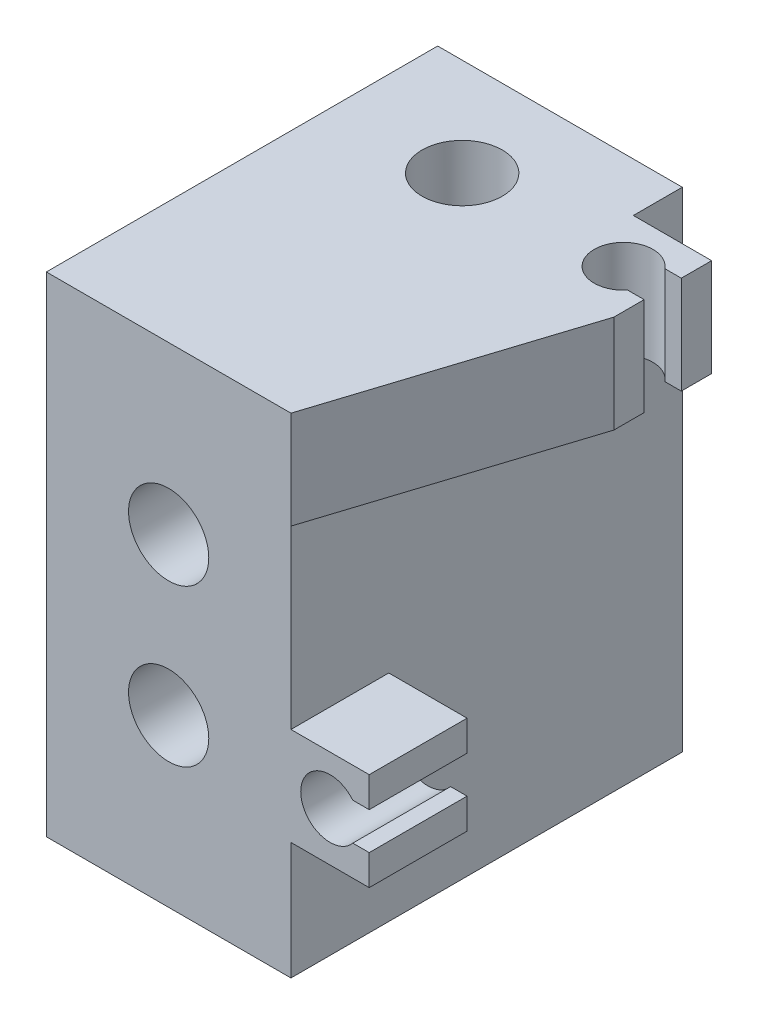
SolidWorks part; units mm, degrees
ref_plane "Спереди" through (0, 0, 0) normal (0, 0, 1) x (1, 0, 0)
ref_plane "Сверху" through (0, 0, 0) normal (0, 1, 0) x (1, 0, 0)
ref_plane "Справа" through (0, 0, 0) normal (1, 0, 0) x (0, 0, -1)
sketch "Sketch1" plane through (0, 0, 0) normal (0, 1, 0) x (1, 0, 0)
  line L1 (12.5, -20) -> (-12.5, -20)
  line L2 (12.5, -20) -> (12.5, 20)
  line L3 (12.5, 20) -> (-12.5, 20)
  line L4 (-12.5, -20) -> (-12.5, 20)
  line L5 (12.5, -20) -> (-12.5, 20) construction
  line L6 (12.5, 20) -> (-12.5, -20) construction
  point P0 (0, 0)
  dimension "D1" = 25
  dimension "D2" = 40
extrude "Boss-Extrude1" add sketch "Sketch1" along normal blind 50
sketch "Sketch2" plane through (0, 0, 0) normal (0, -1, 0) x (1, 0, 0)
  line L0 (12.5, -10) -> (-12.5, -10) construction
  line L1 (12.5, 20) -> (12.5, -20) construction
  line L2 (-12.5, -20) -> (-12.5, 20) construction
  line L3 (12.5, -20) -> (-12.5, -20) construction
  circle A0 centre (0, -10) radius 4.1
  dimension "D1" = 8.2
  dimension "D2" = 10
extrude "Cut-Extrude1" cut sketch "Sketch2" against normal through all
sketch "Sketch3" plane through (0, 0, 20) normal (0, 0, 1) x (1, 0, 0)
  line L0 (0, 0) -> (0, 50) construction
  line L1 (-12.5, 0) -> (12.5, 0) construction
  line L2 (-12.5, 50) -> (12.5, 50) construction
  circle A0 centre (0, 17) radius 4.1
  circle A1 centre (0, 33) radius 4.1
  point P8 (0, 25)
  dimension "D1" = 8.2
  dimension "D2" = 16
  dimension "D3" = 8
extrude "Cut-Extrude2" cut sketch "Sketch3" against normal through all
sketch "Sketch4" plane through (0, 0, -20) normal (0, 0, -1) x (-1, 0, 0)
  line L0 (-12.5, 0) -> (12.5, 0) construction
  line L1 (-7.5, 17) -> (-3.75, 10.5048)
  line L2 (-3.75, 10.5048) -> (3.75, 10.5048)
  line L3 (3.75, 10.5048) -> (7.5, 17)
  line L4 (7.5, 17) -> (3.75, 23.4952)
  line L5 (3.75, 23.4952) -> (-3.75, 23.4952)
  line L6 (-3.75, 23.4952) -> (-7.5, 17)
  line L8 (3.75, 39.4952) -> (-3.75, 39.4952)
  line L9 (-3.75, 39.4952) -> (-7.5, 33)
  line L10 (-7.5, 33) -> (-3.75, 26.5048)
  line L11 (-3.75, 26.5048) -> (3.75, 26.5048)
  line L12 (3.75, 26.5048) -> (7.5, 33)
  line L13 (7.5, 33) -> (3.75, 39.4952)
  circle A0 centre (0, 17) radius 7.5 construction
  circle A1 centre (0, 33) radius 7.5 construction
  dimension "D1" = 15
extrude "Cut-Extrude3" cut sketch "Sketch4" against normal blind 21
sketch "Sketch5" plane through (0, 50, 0) normal (0, 1, 0) x (1, 0, 0)
  line L0 (4.1, 10) -> (27.7656, 10) construction
  line L1 (12.5, -20) -> (12.5, 20) construction
  line L2 (20.5, 5) -> (12.5, 5)
  line L3 (20.5, 5) -> (20.5, 15) construction
  line L4 (20.5, 15) -> (12.5, 15)
  line L5 (12.5, 5) -> (12.5, 15)
  line L6 (20.5, 5) -> (12.5, 15) construction
  line L7 (20.5, 15) -> (12.5, 5) construction
  line L8 (20.5, 15) -> (20.5, 11.9)
  line L9 (20.5, 11.9) -> (18.8216, 11.9)
  line L10 (18.8216, 11.9) -> (18.8216, 8.1)
  line L11 (18.8216, 8.1) -> (20.5, 8.1)
  line L12 (20.5, 8.1) -> (20.5, 5)
  line L13 (-4.1, 10) -> (4.1, 10) construction
  circle A0 centre (0, 10) radius 4.1 construction
  circle A1 centre (16.5, 10) radius 3 construction
  arc A2 (18.8216, 11.9) -> (18.8216, 8.1) centre (16.5, 10) ccw
  point P4 (16.5, 10)
  line M8 (12.5, -20) -> (12.5, 20)
  dimension "D3" = 6
  dimension "D1" = 10
  dimension "D2" = 8
  dimension "D4" = 3.8
extrude "Boss-Extrude2" add sketch "Sketch5" against normal blind 10 contours A2 L9 L8 L4 L2 L12 L11 M8
sketch "Sketch6" plane through (0, 0, 20) normal (0, 0, 1) x (1, 0, 0)
  line L0 (4.1, 17) -> (27.9047, 17) construction
  line L1 (12.5, 50) -> (12.5, 0) construction
  line L2 (20.5, 12) -> (12.5, 12)
  line L3 (20.5, 12) -> (20.5, 22) construction
  line L4 (20.5, 22) -> (12.5, 22)
  line L5 (12.5, 12) -> (12.5, 22)
  line L6 (20.5, 12) -> (12.5, 22) construction
  line L7 (20.5, 22) -> (12.5, 12) construction
  line L8 (20.5, 22) -> (20.5, 18.9)
  line L9 (20.5, 18.9) -> (18.8216, 18.9)
  line L10 (18.8216, 18.9) -> (18.8216, 15.1)
  line L11 (18.8216, 15.1) -> (20.5, 15.1)
  line L12 (20.5, 15.1) -> (20.5, 12)
  circle A0 centre (0, 17) radius 4.1 construction
  circle A1 centre (16.5, 17) radius 3 construction
  arc A2 (18.8216, 18.9) -> (18.8216, 15.1) centre (16.5, 17) ccw
  point P5 (16.5, 17)
  line M10 (12.5, 0) -> (12.5, 50)
  dimension "D3" = 6
  dimension "D1" = 8
  dimension "D2" = 10
  dimension "D4" = 3.8
extrude "Boss-Extrude3" add sketch "Sketch6" against normal blind 10 contours A2 L9 L8 L4 L2 L12 L11 M10
chamfer "Chamfer1" distance 1 angle 45 12 edges at (0, 23.4952, -20) (5.625, 20.2476, -20) (5.625, 13.7524, -20) (0, 10.5048, -20) (-5.625, 13.7524, -20) (-5.625, 20.2476, -20) (-5.625, 36.2476, -20) (0, 39.4952, -20) (5.625, 36.2476, -20) (5.625, 29.7524, -20) (0, 26.5048, -20) (-5.625, 29.7524, -20)
sketch "Sketch7" plane through (0, 50, 0) normal (0, 1, 0) x (1, 0, 0)
  line L0 (20.5, 5) -> (12.5, -20)
  line L1 (12.5, -20) -> (12.5, 5)
  line L2 (12.5, 5) -> (20.5, 5)
extrude "Boss-Extrude4" add sketch "Sketch7" against normal up to surface (10 mm away) up to face at (17.4152, 40, -10)
